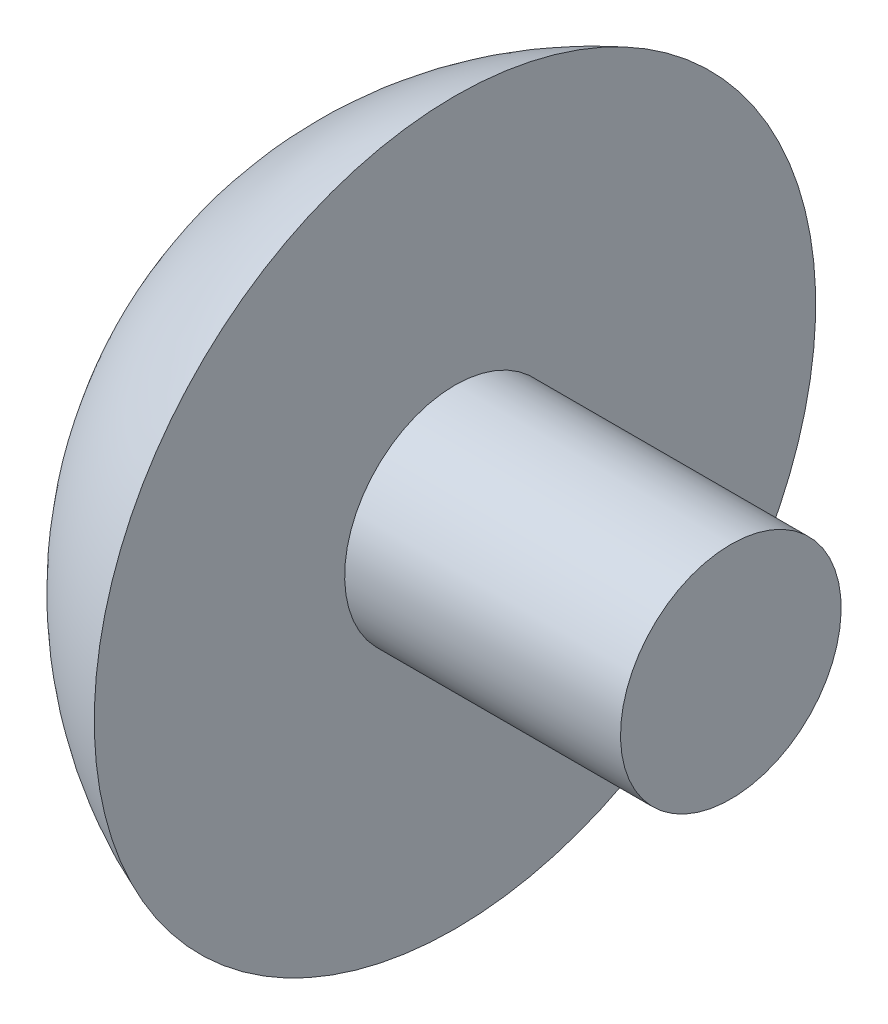
SolidWorks part; units mm, degrees
ref_plane "Plan de face" through (0, 0, 0) normal (0, 0, 1) x (1, 0, 0)
ref_plane "Plan de dessus" through (0, 0, 0) normal (0, 1, 0) x (1, 0, 0)
ref_plane "Plan de droite" through (0, 0, 0) normal (1, 0, 0) x (0, 0, -1)
sketch "Esquisse5" plane through (0, 0, 0) normal (0, 0, 1) x (1, 0, 0)
  line L0 (0, 0) -> (-9.5, 0)
  line L1 (0, 0) -> (0, -2)
  line L2 (0, -2) -> (-5, -2)
  line L3 (-5, -2) -> (-5, -6.5383)
  arc A0 (-9.5, 0) -> (-5, -6.5383) centre (-2.5, 0) ccw
  dimension "D1" = 7
  dimension "D2" = 9.5
  dimension "D3" = 2
  dimension "D4" = 5
revolve "Révolution2" add sketch "Esquisse5" angle 360 about L0
